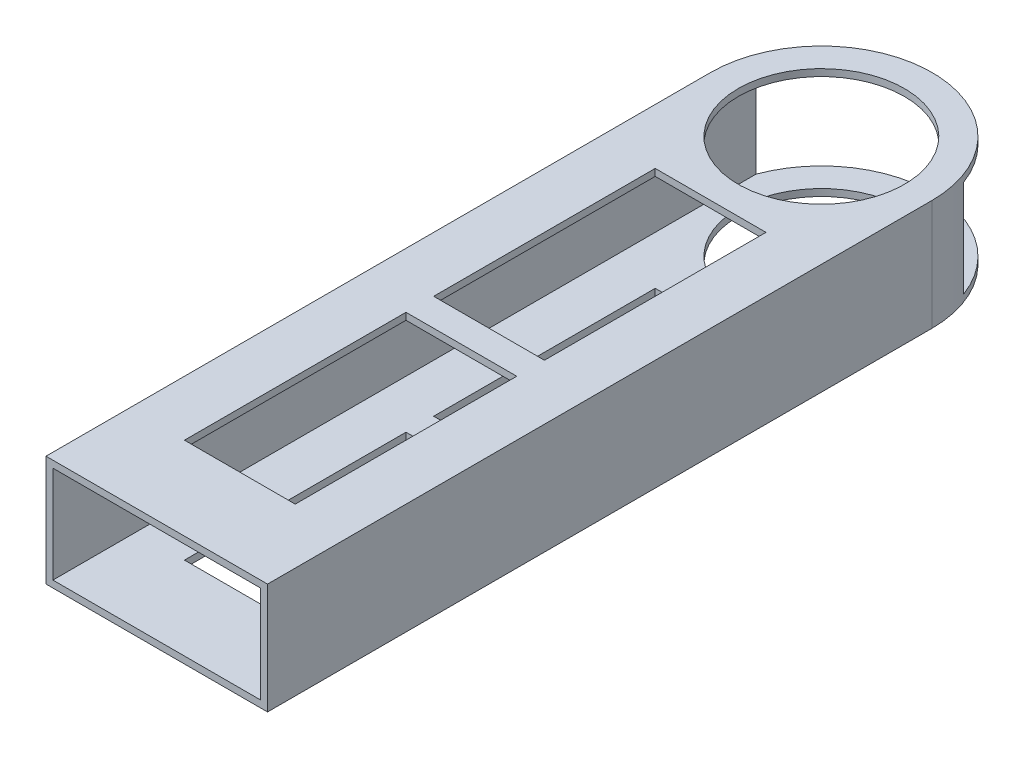
SolidWorks part; units mm, degrees
ref_plane "Front Plane" through (0, 0, 0) normal (0, 0, 1) x (1, 0, 0)
ref_plane "Top Plane" through (0, 0, 0) normal (0, 1, 0) x (1, 0, 0)
ref_plane "Right Plane" through (0, 0, 0) normal (1, 0, 0) x (0, 0, -1)
sketch "Sketch1" plane through (0, 0, 0) normal (0, 0, 1) x (1, 0, 0)
  line L1 (23.8125, -11.1125) -> (-23.8125, -11.1125)
  line L2 (23.8125, -11.1125) -> (23.8125, 11.1125)
  line L3 (23.8125, 11.1125) -> (-23.8125, 11.1125)
  line L4 (-23.8125, -11.1125) -> (-23.8125, 11.1125)
  line L5 (23.8125, -11.1125) -> (-23.8125, 11.1125) construction
  line L6 (23.8125, 11.1125) -> (-23.8125, -11.1125) construction
  line L7 (25.4, -12.7) -> (-25.4, -12.7)
  line L8 (25.4, -12.7) -> (25.4, 12.7)
  line L9 (25.4, 12.7) -> (-25.4, 12.7)
  line L10 (-25.4, -12.7) -> (-25.4, 12.7)
  line L11 (25.4, -12.7) -> (-25.4, 12.7) construction
  line L12 (25.4, 12.7) -> (-25.4, -12.7) construction
  point P0 (0, 0)
  point P6 (0, 0)
  dimension "D1" = 50.8
  dimension "D2" = 25.4
  dimension "D3" = 1.5875
  dimension "D4" = 1.5875
extrude "Boss-Extrude1" add sketch "Sketch1" along normal blind 177.8
sketch "Sketch2" plane through (0, 12.7, 0) normal (0, 1, 0) x (1, 0, 0)
  line L0 (-25.4, -177.8) -> (-25.4, 0) construction
  line L1 (25.4, -177.8) -> (25.4, 0) construction
  line L2 (-25.4, -25.4) -> (25.4, -25.4) construction
  line L3 (-25.4, -25.4) -> (-25.4, 0)
  line L4 (-25.4, 0) -> (25.4, 0)
  line L5 (25.4, 0) -> (25.4, -25.4)
  line L6 (0, 0) -> (0, -177.8) construction
  line L7 (25.4, -177.8) -> (-25.4, -177.8) construction
  line L9 (12.7, -101.6) -> (-12.7, -101.6)
  line L10 (12.7, -101.6) -> (12.7, -50.8)
  line L11 (12.7, -50.8) -> (-12.7, -50.8)
  line L12 (-12.7, -101.6) -> (-12.7, -50.8)
  line L13 (12.7, -101.6) -> (-12.7, -50.8) construction
  line L14 (12.7, -50.8) -> (-12.7, -101.6) construction
  line L15 (12.7, -158.75) -> (-12.7, -158.75)
  line L16 (12.7, -158.75) -> (12.7, -107.95)
  line L17 (12.7, -107.95) -> (-12.7, -107.95)
  line L18 (-12.7, -158.75) -> (-12.7, -107.95)
  line L19 (12.7, -158.75) -> (-12.7, -107.95) construction
  line L20 (12.7, -107.95) -> (-12.7, -158.75) construction
  arc A0 (-25.4, -25.4) -> (25.4, -25.4) centre (0, -25.4) cw
  circle A1 centre (0, -25.4) radius 19.05
  point P17 (0, -76.2)
  point P22 (0, -133.35)
  point P27 (0, -44.45)
  point P28 (0, -50.8)
  point P29 (0, -107.95)
  point P30 (0, -101.6)
  line M2 (25.4, 0) -> (-25.4, 0)
  line M3 (-25.4, 0) -> (-25.4, -177.8)
  line M5 (25.4, -177.8) -> (25.4, 0)
  dimension "D8" = 38.1
  dimension "D1" = 25.4
  dimension "D2" = 50.8
  dimension "D3" = 50.8
  dimension "D4" = 25.4
  dimension "D5" = 25.4
  dimension "D6" = 6.35
  dimension "D7" = 6.35
extrude "Cut-Extrude1" cut sketch "Sketch2" against normal up to surface (25.4 mm away) contours A0 L4 M3 | A1 L2 | A0 M2 M5 | L2 A1 | L18 L15 L16 L17 | L12 L9 L10 L11 up to face at (0, -12.7, 88.9)
